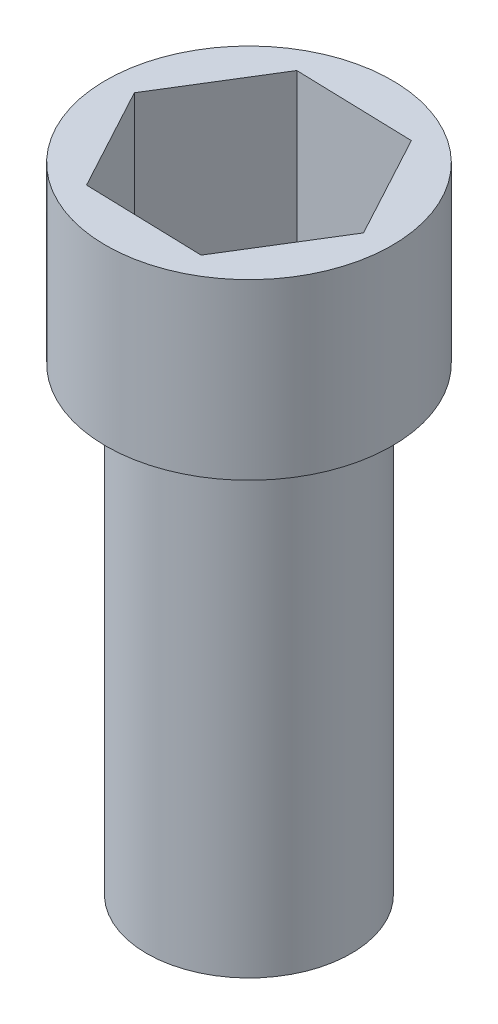
SolidWorks part; units mm, degrees
ref_plane "Front Plane" through (0, 0, 0) normal (0, 0, 1) x (1, 0, 0)
ref_plane "Top Plane" through (0, 0, 0) normal (0, 1, 0) x (1, 0, 0)
ref_plane "Right Plane" through (0, 0, 0) normal (1, 0, 0) x (0, 0, -1)
sketch "Sketch1" plane through (0, 0, 0) normal (0, 1, 0) x (1, 0, 0)
  circle A0 centre (0, 0) radius 10
  dimension "D1" = 20
extrude "Boss-Extrude1" add sketch "Sketch1" along normal blind 45
sketch "Sketch2" plane through (0, 45, 0) normal (0, 1, 0) x (1, 0, 0)
  circle A0 centre (0, 0) radius 14
  dimension "D1" = 28
extrude "Boss-Extrude2" add sketch "Sketch2" along normal blind 2
sketch "Sketch3" plane through (0, 47, 0) normal (0, 1, 0) x (1, 0, 0)
  line L1 (11.5422, -0.3323) -> (6.0589, 9.8297)
  line L2 (6.0589, 9.8297) -> (-5.4833, 10.162)
  line L3 (-5.4833, 10.162) -> (-11.5422, 0.3323)
  line L4 (-11.5422, 0.3323) -> (-6.0589, -9.8297)
  line L5 (-6.0589, -9.8297) -> (5.4833, -10.162)
  line L6 (5.4833, -10.162) -> (11.5422, -0.3323)
  circle A0 centre (0, 0) radius 10 construction
  circle A1 centre (0, 0) radius 14
  circle A2 centre (0, 0) radius 14
  dimension "D2" = 20
  dimension "D1" = 0
extrude "Boss-Extrude3" add sketch "Sketch3" along normal blind 15
